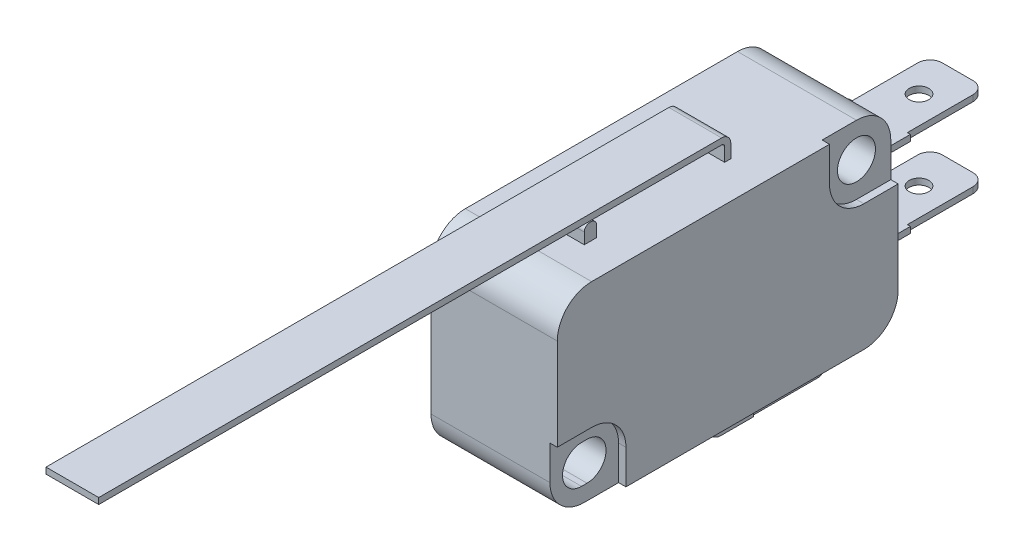
SolidWorks part; units mm, degrees
ref_plane "Front Plane" through (0, 0, 0) normal (0, 0, 1) x (1, 0, 0)
ref_plane "Top Plane" through (0, 0, 0) normal (0, 1, 0) x (1, 0, 0)
ref_plane "Right Plane" through (0, 0, 0) normal (1, 0, 0) x (0, 0, -1)
sketch "Sketch1" plane through (0, 0, 0) normal (1, 0, 0) x (0, 0, -1)
  line L1 (-13.9, -7.95) -> (13.9, -7.95)
  line L2 (-13.9, -7.95) -> (-13.9, 7.95)
  line L3 (-13.9, 7.95) -> (13.9, 7.95)
  line L4 (13.9, -7.95) -> (13.9, 7.95)
  line L5 (-13.9, -7.95) -> (13.9, 7.95) construction
  line L6 (-13.9, 7.95) -> (13.9, -7.95) construction
  point P0 (0, 0)
  dimension "D1" = 27.8
  dimension "D2" = 15.9
extrude "Boss-Extrude1" add sketch "Sketch1" along normal mid plane 10.3
sketch "Sketch4" plane through (5.15, 0, 0) normal (1, 0, 0) x (0, 0, -1)
  line L0 (13.9, 7.95) -> (-13.9, 7.95) construction
  line L1 (13.9, -7.95) -> (13.9, 7.95) construction
  line L2 (-11.325, -5.15) -> (-10.875, -5.15) construction
  line L3 (-11.325, -3.6) -> (-10.875, -3.6)
  line L4 (-11.325, -6.7) -> (-10.875, -6.7)
  circle A0 centre (11.1, 5.15) radius 1.55
  arc A1 (-11.325, -3.6) -> (-11.325, -6.7) centre (-11.325, -5.15) ccw
  arc A2 (-10.875, -6.7) -> (-10.875, -3.6) centre (-10.875, -5.15) ccw
  point P8 (-11.1, -5.15)
  dimension "D1" = 3.1
  dimension "D2" = 2.8
  dimension "D3" = 2.8
  dimension "D4" = 3.1
  dimension "D5" = 0.45
  dimension "D6" = 22.2
  dimension "D7" = 10.3
extrude "Cut-Extrude1" cut sketch "Sketch4" against normal through all
sketch "Sketch5" plane through (5.15, 0, 0) normal (1, 0, 0) x (0, 0, -1)
  line L0 (-12.875, -5.15) -> (-9.325, -5.15) construction
  line L4 (-11.1, -3.6) -> (-11.1, -6.7) construction
  line L5 (13.9, 2.35) -> (-13.9, 2.35)
  line L6 (13.9, 2.35) -> (11.1, 2.35)
  line L7 (-10.875, -3.6) -> (-11.325, -3.6) construction
  line L8 (-11.325, -6.7) -> (-10.875, -6.7) construction
  line L10 (-13.9, -2.35) -> (13.9, -2.35)
  line L11 (-13.9, -2.35) -> (-11.1, -2.35)
  line L12 (-8.3, -5.15) -> (-8.3, -7.95)
  line L19 (8.3, 5.15) -> (8.3, 7.95)
  line L20 (-13.9, -2.35) -> (-13.9, -7.95)
  line L21 (-13.9, -7.95) -> (-8.3, -7.95)
  line L22 (8.3, 7.95) -> (13.9, 7.95)
  line L23 (13.9, 7.95) -> (13.9, 2.35)
  arc A0 (-11.325, -3.6) -> (-11.325, -6.7) centre (-11.325, -5.15) ccw construction
  arc A1 (-10.875, -6.7) -> (-10.875, -3.6) centre (-10.875, -5.15) ccw construction
  arc A2 (11.1, 2.35) -> (8.3, 5.15) centre (11.1, 5.15) cw
  arc A3 (-8.3, -5.15) -> (-11.1, -2.35) centre (-11.1, -5.15) ccw
  dimension "D5" = 2.8
  dimension "D3" = 5.6
  dimension "D2" = 5.6
extrude "Cut-Extrude2" cut sketch "Sketch5" against normal blind 0.6
ref_plane "Plane1" through (0, 2.45, 0) normal (0, 1, 0) x (1, 0, 0)
sketch "Sketch8" plane through (0, 2.45, 0) normal (0, 1, 0) x (1, 0, 0)
  line L0 (-2.5, 13.9) -> (2.5, 13.9)
  line L1 (0, 13.0007) -> (0, 24.4566) construction
  line L2 (4.55, 13.9) -> (-5.15, 13.9) construction
  line L3 (2.5, 13.9) -> (2.5, 17.55)
  line L4 (2.5, 17.55) -> (2.25, 17.55)
  line L5 (2.25, 17.55) -> (2.25, 23.9)
  line L6 (2.25, 23.9) -> (-2.25, 23.9)
  line L7 (-2.5, 17.55) -> (-2.25, 17.55)
  line L8 (-2.5, 13.9) -> (-2.5, 17.55)
  line L9 (-2.25, 17.55) -> (-2.25, 23.9)
  circle A0 centre (0, 20.75) radius 0.8
  point P12 (0, 23.9)
  point P13 (0, 13.9)
  dimension "D4" = 1.6
  dimension "D1" = 2.5
  dimension "D2" = 3.65
  dimension "D3" = 0.25
  dimension "D5" = 3.2
extrude "Boss-Extrude2" add sketch "Sketch8" along normal mid plane 0.5
pattern_linear "LPattern1" count 2 spacing 6.5 along (0, -1, 0) of "Boss-Extrude2"
ref_plane "Plane4" through (2.5, 0, 0) normal (1, 0, 0) x (0, 0, -1)
sketch "Sketch9" plane through (2.5, 0, 0) normal (1, 0, 0) x (0, 0, -1)
  line L0 (11.1, 5.15) -> (11.1, -14.4152) construction
  line L1 (1.1, 5.15) -> (1.1, -14.4152) construction
  line L3 (1.1, -7.95) -> (1.1, -9.85)
  line L4 (2.1, -10.85) -> (4.75, -10.85)
  line L5 (1.6, -7.95) -> (1.6, -9.85)
  line L6 (-8.3, -7.95) -> (13.9, -7.95) construction
  line L7 (2.1, -10.35) -> (4.75, -10.35)
  line L8 (1.1, -7.95) -> (1.6, -7.95)
  line L9 (4.75, -10.85) -> (4.75, -10.35)
  arc A0 (1.1, -9.85) -> (2.1, -10.85) centre (2.1, -9.85) ccw
  arc A1 (1.6, -9.85) -> (2.1, -10.35) centre (2.1, -9.85) ccw
  dimension "D3" = 1
  dimension "D1" = 10
  dimension "D2" = 2.65
extrude "Boss-Extrude3" add sketch "Sketch9" against normal blind 5
sketch "Sketch10" plane through (0, 0, -4.75) normal (0, 0, -1) x (-1, 0, 0)
  line L0 (0, -10.1645) -> (0, -11.1143) construction
  line L1 (2.5, -10.6) -> (-2.5, -10.6) construction
  line L2 (2.5, -10.85) -> (2.5, -10.35) construction
  line L3 (-2.5, 3.518) -> (-2.5, -3.518) construction
  line L4 (2.5, -10.35) -> (-2.5, -10.35) construction
  line L5 (-2.375, -10.85) -> (2.375, -10.85)
  line L6 (-2.375, -10.85) -> (-2.375, -10.35)
  line L7 (-2.375, -10.35) -> (2.375, -10.35)
  line L8 (2.375, -10.85) -> (2.375, -10.35)
  line L9 (-2.375, -10.85) -> (2.375, -10.35) construction
  line L10 (-2.375, -10.35) -> (2.375, -10.85) construction
  point P9 (0, -10.6)
  dimension "D1" = 4.75
extrude "Boss-Extrude4" add sketch "Sketch10" along normal blind 6.35
sketch "Sketch11" plane through (0, -10.85, 0) normal (0, -1, 0) x (1, 0, 0)
  line L0 (2.375, -4.75) -> (2.5, -4.75) construction
  circle A0 centre (0, -7.95) radius 0.8
  dimension "D1" = 1.6
  dimension "D2" = 3.2
extrude "Cut-Extrude3" cut sketch "Sketch11" against normal up to next
sketch "Sketch12" plane through (0, 0, 0) normal (1, 0, 0) x (0, 0, -1)
  line L4 (3.25, 7.95) -> (3.25, 9.05)
  line L5 (2.5, 9.8) -> (-48.3, 9.8)
  line L6 (2.75, 7.95) -> (2.75, 9.05)
  line L7 (2.5, 9.3) -> (-48.3, 9.3)
  line L8 (3.25, 7.95) -> (2.75, 7.95)
  line L9 (-48.3, 9.8) -> (-48.3, 9.3)
  arc A2 (3.25, 9.05) -> (2.5, 9.8) centre (2.5, 9.05) ccw
  arc A3 (2.75, 9.05) -> (2.5, 9.3) centre (2.5, 9.05) ccw
extrude "Boss-Extrude5" add sketch "Sketch12" along normal mid plane 4.3
sketch "Sketch13" plane through (0, 0, 0) normal (1, 0, 0) x (0, 0, -1)
  line L0 (-8.3, 9.3) -> (-8.3, 7.95) construction
  line L1 (-13.9, 7.95) -> (-13.9, -2.35) construction
  line L2 (-48.3, 9.3) -> (2.5, 9.3) construction
  line L3 (8.3, 7.95) -> (-13.9, 7.95) construction
  line L4 (-8.8, 8.85) -> (-8.8, 7.95)
  line L5 (-8.35, 9.3) -> (-8.25, 9.3)
  line L6 (-8.8, 7.95) -> (-7.8, 7.95)
  line L7 (-7.8, 8.85) -> (-7.8, 7.95)
  line L8 (-8.8, 9.3) -> (-7.8, 7.95) construction
  line L9 (-8.8, 7.95) -> (-7.8, 9.3) construction
  arc A0 (-8.35, 9.3) -> (-8.8, 8.85) centre (-8.35, 8.85) ccw
  arc A1 (-8.25, 9.3) -> (-7.8, 8.85) centre (-8.25, 8.85) cw
  point P9 (-8.3, 8.625)
  dimension "D3" = 0.45
  dimension "D1" = 5.6
  dimension "D2" = 1
extrude "Boss-Extrude7" add sketch "Sketch13" along normal mid plane 4.5
fillet "Fillet1" radius 2.8 4 edges at (-0.3, -7.95, 13.9) (0, 7.95, 13.9) (0, -7.95, -13.9) (-0.3, 7.95, -13.9)
fillet "Fillet2" radius 1 6 edges at (2.375, -10.6, -11.1) (-2.375, -10.6, -11.1) (2.25, -4.05, -23.9) (-2.25, -4.05, -23.9) (-2.25, 2.45, -23.9) (2.25, 2.45, -23.9)
